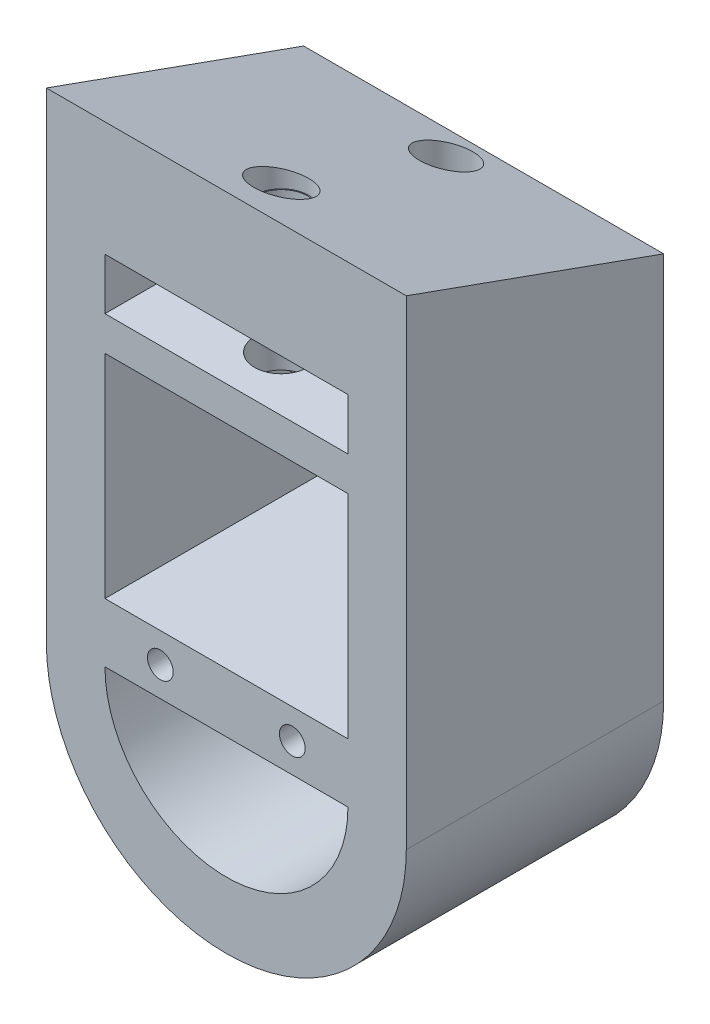
SolidWorks part; units mm, degrees
ref_plane "Front Plane" through (0, 0, 0) normal (0, 0, 1) x (1, 0, 0)
ref_plane "Top Plane" through (0, 0, 0) normal (0, 1, 0) x (1, 0, 0)
ref_plane "Right Plane" through (0, 0, 0) normal (1, 0, 0) x (0, 0, -1)
sketch "Sketch2" plane through (0, 0, 0) normal (0, 0, 1) x (1, 0, 0)
  line L0 (0, 0) -> (0, -15) construction
  line L1 (10.489, 0) -> (10.489, -15)
  line L2 (-10.489, 0) -> (-10.489, -15)
  line L3 (0.0079, -0.4333) -> (0.0079, -14.5468) construction
  line L6 (7.089, -0.4333) -> (7.089, -14.5468)
  line L7 (-7.0732, -0.4333) -> (-7.0732, -14.5468)
  line L8 (0, 10.489) -> (15.1947, 10.489)
  line L9 (0, -25.489) -> (18.3702, -25.489)
  line L10 (0, -11.0366) -> (0, -16.2959)
  line L11 (-7.0732, -11.1068) -> (7.089, -11.1068)
  line L12 (-7.0732, -11.1068) -> (-7.0732, -14.5468)
  line L13 (-7.0732, -14.5468) -> (7.089, -14.5468)
  line L14 (7.089, -11.1068) -> (7.089, -14.5468)
  line L20 (7.089, -2.7773) -> (-7.0732, -2.7773)
  line L21 (7.089, -2.7773) -> (7.089, -6.1773)
  line L22 (7.089, -6.1773) -> (-7.0732, -6.1773)
  line L23 (-7.0732, -2.7773) -> (-7.0732, -6.1773)
  arc A0 (10.489, 0) -> (-10.489, 0) centre (0, 0) ccw
  arc A1 (-10.489, -15) -> (10.489, -15) centre (0, -15) ccw
  arc A4 (7.089, -0.4333) -> (-7.0732, -0.4333) centre (0.0079, -0.4333) ccw
  arc A5 (-7.0732, -14.5468) -> (7.089, -14.5468) centre (0.0079, -14.5468) ccw
  circle A6 centre (-3.8453, -12.8375) radius 0.75
  circle A7 centre (3.8453, -12.8375) radius 0.75
  point P3 (0, -7.5)
  point P10 (0.0079, -7.49)
  dimension "D4" = 1.5
  dimension "D1" = 15
  dimension "D2" = 3.4
  dimension "D3" = 3.44
  dimension "D5" = 3.4
extrude "Boss-Extrude1" add sketch "Sketch2" along normal blind 20 contours L2 A1 L1 A0 A5 L7 A4 L6 | L7 L22 L6 L20 | L7 L13 L10 L11 A6 | L10 L13 L6 L11 A7
sketch "Sketch5" plane through (0, 0, 0) normal (1, 0, 0) x (0, 0, -1)
  line L0 (-20, 10.489) -> (-20, 13.7769)
  line L1 (-20, 13.7769) -> (0, 10.489)
  line L2 (0, 10.489) -> (-20, 10.489)
extrude "Boss-Extrude2" add sketch "Sketch5" along normal blind 23 from offset 11 separate body offset against normal yes
sketch "Sketch6" plane through (0, 0, 0) normal (0, 0, 1) x (1, 0, 0)
  line L0 (-10.489, 0) -> (-10.489, 15.8603)
  line L1 (-10.489, 15.8603) -> (-12.4862, 15.8603)
  line L2 (-12.4862, 15.8603) -> (-12.4862, -0.6958)
  line L3 (-12.4862, -0.6958) -> (-10.489, 0)
  line L4 (10.489, 0) -> (10.489, 17.1409)
  line L5 (10.489, 17.1409) -> (14.4518, 17.1409)
  line L6 (14.4518, 17.1409) -> (14.0859, 0)
  line L7 (14.0859, 0) -> (10.489, 0)
extrude "Cut-Extrude1" cut sketch "Sketch6" along normal blind 23
sketch "Sketch7" plane through (0, 0, 0) normal (0, 0, 1) x (1, 0, 0)
  line L0 (-10.489, 10.489) -> (-10.489, 0)
  line L1 (-10.489, 0) -> (-4.0069, 9.1179)
  line L2 (-4.0069, 9.1179) -> (3.3933, 9.1179)
  line L3 (3.3933, 9.1179) -> (10.489, 0)
  line L4 (10.489, 0) -> (10.489, 10.489)
  line L5 (10.489, 10.489) -> (-10.489, 10.489)
extrude "Boss-Extrude3" add sketch "Sketch7" along normal blind 20
sketch "Sketch8" plane through (0, 0, 0) normal (0, 1, 0) x (1, 0, 0)
  circle A0 centre (0, -11.796) radius 1.6
  dimension "D1" = 3.2
extrude "Cut-Extrude2" cut sketch "Sketch8" along normal blind 50
sketch "Sketch9" plane through (0, 0, 0) normal (0, 0, 1) x (1, 0, 0)
  line L0 (0, -19.8966) -> (0, 19.8966) construction
  line L1 (10.489, 13.7769) -> (-10.489, 13.7769) construction
  line L2 (-7.5, 10.3769) -> (7.5, 10.3769)
  line L3 (-7.5, 10.3769) -> (-7.5, 7.3769)
  line L4 (-7.5, 7.3769) -> (7.5, 7.3769)
  line L5 (7.5, 10.3769) -> (7.5, 7.3769)
  line L6 (-7.5, 10.3769) -> (7.5, 7.3769) construction
  line L7 (-7.5, 7.3769) -> (7.5, 10.3769) construction
  point P0 (0, 8.8769)
  point P4 (0, 0)
  dimension "D1" = 3
  dimension "D2" = 15
  dimension "D3" = 3.4
extrude "Cut-Extrude3" cut sketch "Sketch9" along normal blind 50 from offset 9 contours L3 L2 L5 L4
sketch "Sketch10" plane through (0, 0, 0) normal (0, 0, 1) x (1, 0, 0)
  line L0 (7.089, -2.7773) -> (-7.0732, -2.7773) construction
  line L1 (4, -2.7773) -> (-4, -2.7773)
  line L2 (4, -2.7773) -> (4, -6.1773)
  line L3 (4, -6.1773) -> (-4, -6.1773)
  line L4 (-4, -2.7773) -> (-4, -6.1773)
  line L5 (7.089, -6.1773) -> (-7.0732, -6.1773) construction
  line L6 (0, 8.3202) -> (0, -8.3202) construction
  point P12 (0, 0)
  dimension "D1" = 8
  dimension "D2" = 4
  dimension "D3" = 3.4
extrude "Boss-Extrude4" add sketch "Sketch10" against normal blind 20
sketch "Sketch11" plane through (0, 0, 0) normal (0, 1, 0) x (1, 0, 0)
  line L0 (-4, 27.9335) -> (-5.6691, 15.9926)
  line L1 (5.5574, 15.4744) -> (4, 27.9335)
  line L2 (5.5574, 15.4744) -> (-5.6691, 15.9926)
  line L3 (-4, 20) -> (-4, 0) construction
  line L4 (4, 20) -> (4, 0) construction
  circle A0 centre (0, 27.9335) radius 4
extrude "Cut-Extrude4" cut sketch "Sketch11" against normal blind 15 contours A0 L1 L2 L0
sketch "Sketch12" plane through (0, 0, 0) normal (0, 1, 0) x (1, 0, 0)
  line L0 (0, -15.646) -> (0, 15.646) construction
  line L1 (7.089, 0) -> (4, 0) construction
  line L6 (1.5, 0) -> (-1.5, 0)
  line L7 (1.5, 0) -> (1.5, 10.0354)
  line L8 (1.5, 10.0354) -> (-1.5, 10.0354)
  line L9 (-1.5, 0) -> (-1.5, 10.0354)
  line L10 (1.5, 0) -> (-1.5, 10.0354) construction
  line L11 (1.5, 10.0354) -> (-1.5, 0) construction
  circle A0 centre (0, 10) radius 1.5
  point P0 (0, 5.0177)
  point P4 (0, 0)
  dimension "D1" = 3
  dimension "D2" = 0
  dimension "D3" = 10
extrude "Cut-Extrude6" cut sketch "Sketch12" against normal blind 15 contours A0 L8 | L8 A0 | A0 L9 L6 L7
sketch "Sketch13" plane through (0, 0, 0) normal (0, 1, 0) x (1, 0, 0)
  line L0 (-4, 10.0243) -> (-7.4391, 19.1785)
  line L1 (-7.4391, 19.1785) -> (9.6681, 17.5137)
  line L2 (9.6681, 17.5137) -> (4, 10.0243)
  circle A0 centre (0, 10.0243) radius 4
extrude "Cut-Extrude7" cut sketch "Sketch13" against normal through all and the other way through all contours A0 L2 L1 L0
sketch "Sketch14" plane through (0, 0, 0) normal (1, 0, 0) x (0, 0, -1)
  line L0 (-15, 13.7239) -> (-26.7301, 15.4225)
  line L1 (0, -25.489) -> (-15, -25.489)
  line L2 (0, -25.489) -> (0, 13.7239)
  line L3 (0, 13.7239) -> (-15, 13.7239)
  line L4 (-15, -25.489) -> (-15, 13.7239)
  line L5 (-26.7301, 15.4225) -> (-23.0369, -28.4462)
  line L6 (-23.0369, -28.4462) -> (-15, -25.489)
  dimension "D1" = 15
extrude "Cut-Extrude8" cut sketch "Sketch14" against normal through all both and the other way through all contours L5 L6 L4 L0
sketch "Sketch15" plane through (0, 0, 0) normal (1, 0, 0) x (0, 0, -1)
  line L0 (-15, 12.9549) -> (0, 7.5735)
  line L1 (0, 10.489) -> (0, -15) construction
  line L2 (0, 7.5735) -> (5.5215, 8.8243)
  line L3 (5.5215, 8.8243) -> (5.5215, 13.5013)
  line L4 (5.5215, 13.5013) -> (-15.1441, 13.9907)
  line L5 (-15.1441, 13.9907) -> (-15, 12.9549)
extrude "Cut-Extrude9" cut sketch "Sketch15" against normal through all both and the other way through all
sketch "Sketch16" plane through (0, 0, 0) normal (0, 0, 1) x (1, 0, 0)
  line L1 (-7.0732, -2.7773) -> (7.089, -2.7773)
  line L2 (-7.0732, -2.7773) -> (-7.0732, 6.5998)
  line L3 (-7.0732, 6.5998) -> (7.089, 6.5998)
  line L4 (7.089, -2.7773) -> (7.089, 6.5998)
extrude "Cut-Extrude10" cut sketch "Sketch16" against normal through all both and the other way through all
sketch "Sketch17" plane through (0, 0, 0) normal (0, 0, 1) x (1, 0, 0)
  line L0 (7.089, 6.2716) -> (-7.0732, 6.2716)
  line L1 (7.089, 6.5998) -> (7.089, -2.7773) construction
  line L2 (-7.0732, 6.5998) -> (-7.0732, -2.7773) construction
  line L3 (-7.0732, 6.2716) -> (-7.0732, 6.5998)
  line L4 (7.089, 6.2716) -> (7.089, 6.9348)
  line L5 (7.089, 6.9348) -> (-7.0732, 6.9348)
  line L6 (-7.0732, 6.9348) -> (-7.0732, 6.4357)
extrude "Boss-Extrude5" add sketch "Sketch17" along normal through all contours L5 L6 L3 L0 L4
sketch "Sketch18" plane through (0, 0, 0) normal (0, 0, 1) x (1, 0, 0)
  line L0 (-7.0732, -2.7773) -> (-7.0732, 6.2716) construction
  line L1 (-7.0732, 3.2716) -> (7.089, 3.2716)
  line L2 (-7.0732, 3.2716) -> (-7.0732, 1.2716)
  line L3 (-7.0732, 1.2716) -> (7.089, 1.2716)
  line L4 (7.089, 3.2716) -> (7.089, 1.2716)
  line L5 (7.089, -2.7773) -> (7.089, 6.2716) construction
  line L6 (7.089, 6.2716) -> (-7.0732, 6.2716) construction
  dimension "D1" = 3
  dimension "D2" = 2
extrude "Boss-Extrude6" add sketch "Sketch18" along normal through all
sketch "Sketch19" plane through (0, 0, 0) normal (0, 0, 1) x (1, 0, 0)
  line L1 (-7.5, 10.3769) -> (7.5, 10.3769)
  line L2 (-7.5, 10.3769) -> (-7.5, 7.3769)
  line L3 (-7.5, 7.3769) -> (7.5, 7.3769)
  line L4 (7.5, 10.3769) -> (7.5, 7.3769)
extrude "Boss-Extrude7" add sketch "Sketch19" along normal through all
sketch "Sketch20" plane through (0, 0, 0) normal (1, 0, 0) x (0, 0, -1)
  line L0 (-15, 12.9549) -> (0, 7.5735)
  line L1 (0, 7.5735) -> (2.5343, 12.9549)
  line L2 (2.5343, 12.9549) -> (-15, 12.9549)
extrude "Cut-Extrude11" cut sketch "Sketch20" against normal through all both and the other way through all
sketch "Sketch21" plane through (0, 0, 0) normal (0, 1, 0) x (1, 0, 0)
  circle A0 centre (0, -11.8057) radius 1.55
  point P2 (0, -10.9051)
  point P3 (0, -11.7819)
  point P4 (0, -11.8057)
  dimension "D1" = 3.1
extrude "Cut-Extrude12" cut sketch "Sketch21" along normal blind 20
sketch "Sketch23" plane through (0, 0, 0) normal (0, 0, 1) x (1, 0, 0)
  line L1 (-7.0732, 1.2716) -> (7.089, 1.2716)
  line L2 (-7.0732, 1.2716) -> (-7.0732, -11.1068)
  line L3 (-7.0732, -11.1068) -> (7.089, -11.1068)
  line L4 (7.089, 1.2716) -> (7.089, -11.1068)
extrude "Cut-Extrude13" cut sketch "Sketch23" against normal through all both and the other way through all
sketch "Sketch24" plane through (0, 0, 0) normal (0, 0, 1) x (1, 0, 0)
  line L0 (-7.0732, -11.1068) -> (-7.0732, 1.2716) construction
  line L1 (-7.0732, -1.7284) -> (7.089, -1.7284)
  line L2 (-7.0732, -1.7284) -> (-7.0732, -4.2284)
  line L3 (-7.0732, -4.2284) -> (7.089, -4.2284)
  line L4 (7.089, -1.7284) -> (7.089, -4.2284)
  line L5 (7.089, -11.1068) -> (7.089, 1.2716) construction
  line L6 (-7.0732, 1.2716) -> (7.089, 1.2716) construction
  dimension "D1" = 3
  dimension "D2" = 2.5
extrude "Boss-Extrude8" add sketch "Sketch24" along normal blind 5
sketch "Sketch25" plane through (0, 0, 0) normal (0, 1, 0) x (1, 0, 0)
  circle A0 centre (0, -2.1914) radius 1.55
  point P2 (0, -2.1914)
  dimension "D1" = 3.1
extrude "Cut-Extrude14" cut sketch "Sketch25" along normal blind 20 from offset 10
